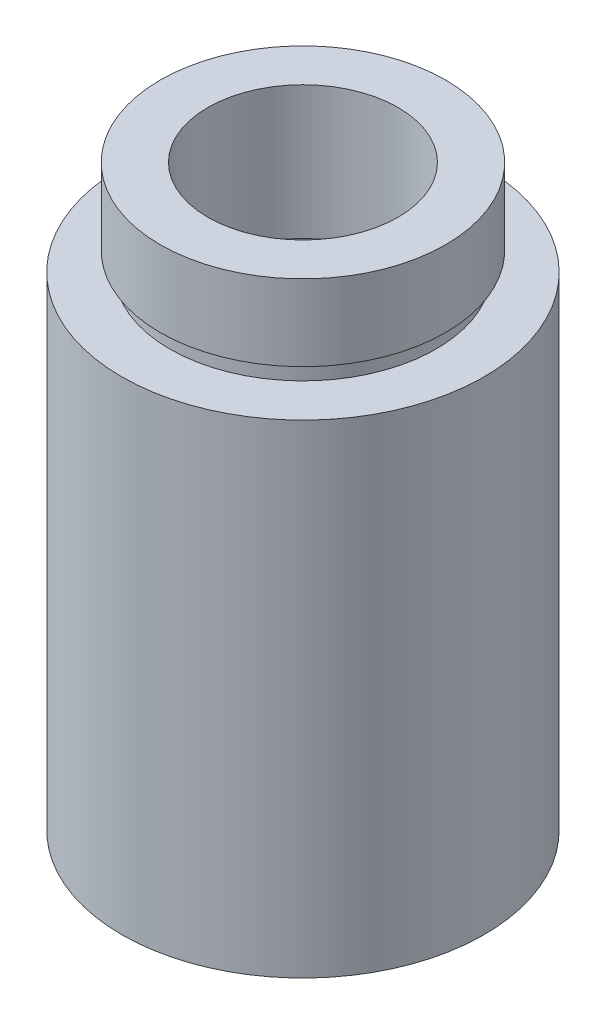
SolidWorks part; units mm, degrees
ref_plane "前视基准面" through (0, 0, 0) normal (0, 0, 1) x (1, 0, 0)
ref_plane "上视基准面" through (0, 0, 0) normal (0, 1, 0) x (1, 0, 0)
ref_plane "右视基准面" through (0, 0, 0) normal (1, 0, 0) x (0, 0, -1)
sketch "草图1" plane through (0, 0, 0) normal (0, 0, 1) x (1, 0, 0)
  line L0 (0, 161.3762) -> (0, 0) construction
  line L1 (141.7365, 0) -> (-131.7984, 0) construction
  line L2 (7, 26.4) -> (7.5, 26.4)
  line L3 (6.85, 23.4) -> (6.85, 22.4)
  line L4 (5, 23.4) -> (6.85, 23.4)
  line L5 (5, 23.4) -> (5, 30.4)
  line L6 (7.5, 26.4) -> (7.5, 30.4)
  line L7 (9.525, 25.4) -> (9.525, 0)
  line L8 (9.525, 0) -> (7, 0)
  line L9 (7, 0) -> (7, 4.5)
  line L10 (7, 25.4) -> (9.525, 25.4)
  line L11 (5, 30.4) -> (7.5, 30.4)
  line L12 (6.75, 22.4) -> (6.85, 22.4)
  line L13 (7, 26.4) -> (7, 25.4)
  line L14 (6.75, 5.5) -> (6.75, 22.4)
  line L15 (7, 4.5) -> (7.6, 4.5)
  line L16 (7.6, 4.5) -> (7.6, 5.5)
  line L17 (6.75, 5.5) -> (7.6, 5.5)
  dimension "D2" = 25.4
  dimension "D3" = 1
  dimension "D4" = 4.5
  dimension "D5" = 5
  dimension "D6" = 7.5
  dimension "D7" = 7
  dimension "D8" = 1
  dimension "D9" = 7
  dimension "D10" = 4
  dimension "D11" = 9.525
  dimension "D12" = 7.6
  dimension "D13" = 6.85
  dimension "D14" = 7
  dimension "D15" = 6.75
  dimension "D16" = 1
revolve "旋转1" add sketch "草图1" angle 360 about L0
cosmetic thread "装饰螺纹线1" parameters "D2"=15
cosmetic thread "装饰螺纹线2" parameters "D2"=13.51
cosmetic thread "装饰螺纹线3" parameters "D2"=14.99
cosmetic thread "装饰螺纹线4" parameters "D2"=11
